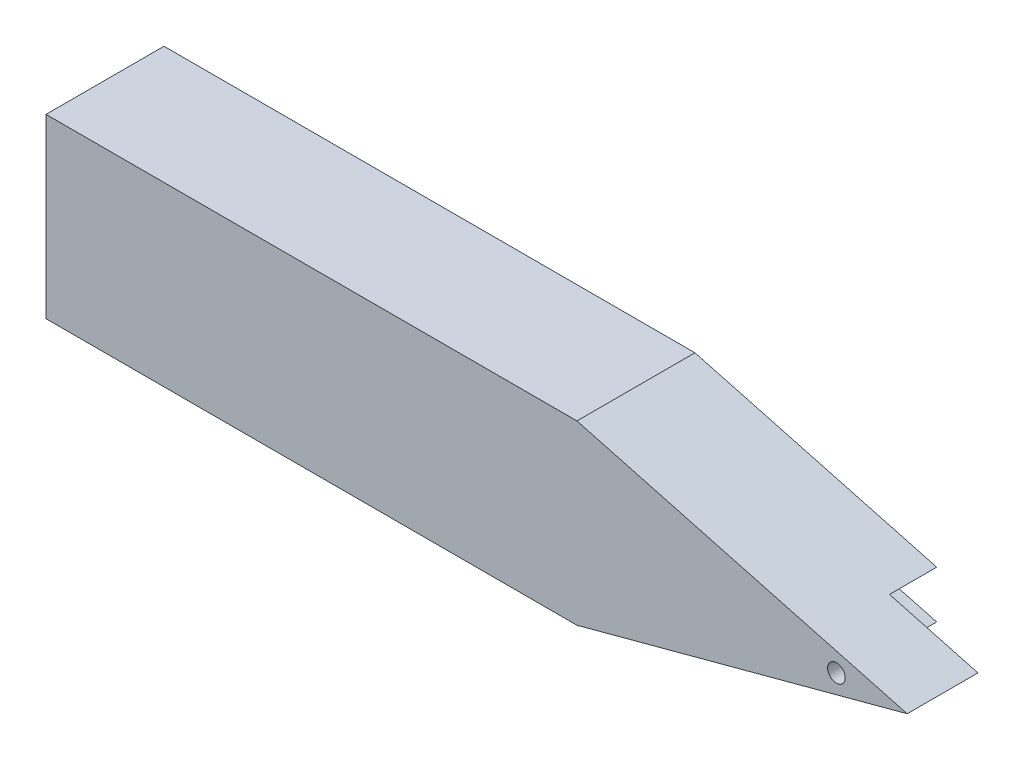
SolidWorks part; units mm, degrees
ref_plane "前视基准面" through (0, 0, 0) normal (0, 0, 1) x (1, 0, 0)
ref_plane "上视基准面" through (0, 0, 0) normal (0, 1, 0) x (1, 0, 0)
ref_plane "右视基准面" through (0, 0, 0) normal (1, 0, 0) x (0, 0, -1)
sketch "草图1" plane through (0, 0, 0) normal (0, 0, 1) x (1, 0, 0)
  line L0 (47.5, 15) -> (103.4808, 0)
  line L1 (-42.5, -15) -> (47.5, -15)
  line L2 (-42.5, -15) -> (-42.5, 15)
  line L3 (-42.5, 15) -> (47.5, 15)
  line L6 (-42.5, 15) -> (4.4724, -1.5785) construction
  line L7 (103.4808, 0) -> (47.5, -15)
  point P0 (0, 0)
  dimension "D1" = 90
  dimension "D2" = 30
  dimension "D3" = 195
  dimension "D4" = 30
  dimension "D5" = 15
  dimension "D6" = 47.5
extrude "凸台-拉伸1" add sketch "草图1" along normal blind 20
sketch "草图2" plane through (0, 0, 0) normal (0, 0, -1) x (-1, 0, 0)
  line L0 (-88.4808, 4.0192) -> (-73.4808, 0)
  line L1 (-103.4808, 0) -> (-47.5, 15) construction
  line L2 (-73.4808, 0) -> (-88.4808, -4.0192)
  line L3 (-47.5, -15) -> (-103.4808, 0) construction
  line L4 (-88.4808, 4.0192) -> (-103.4808, 0)
  line L5 (-103.4808, 0) -> (-88.4808, -4.0192)
  dimension "D1" = 15
extrude "切除-拉伸1" cut sketch "草图2" against normal blind 8
sketch "草图4" plane through (0, 0, 8) normal (0, 0, -1) x (-1, 0, 0)
  circle A0 centre (-91.4808, 0) radius 1.5
  dimension "D1" = 3
  dimension "D2" = 12
extrude "切除-拉伸2" cut sketch "草图4" against normal through all
cosmetic thread "装饰螺纹线1" parameters "D1"=12, "D2"=9
